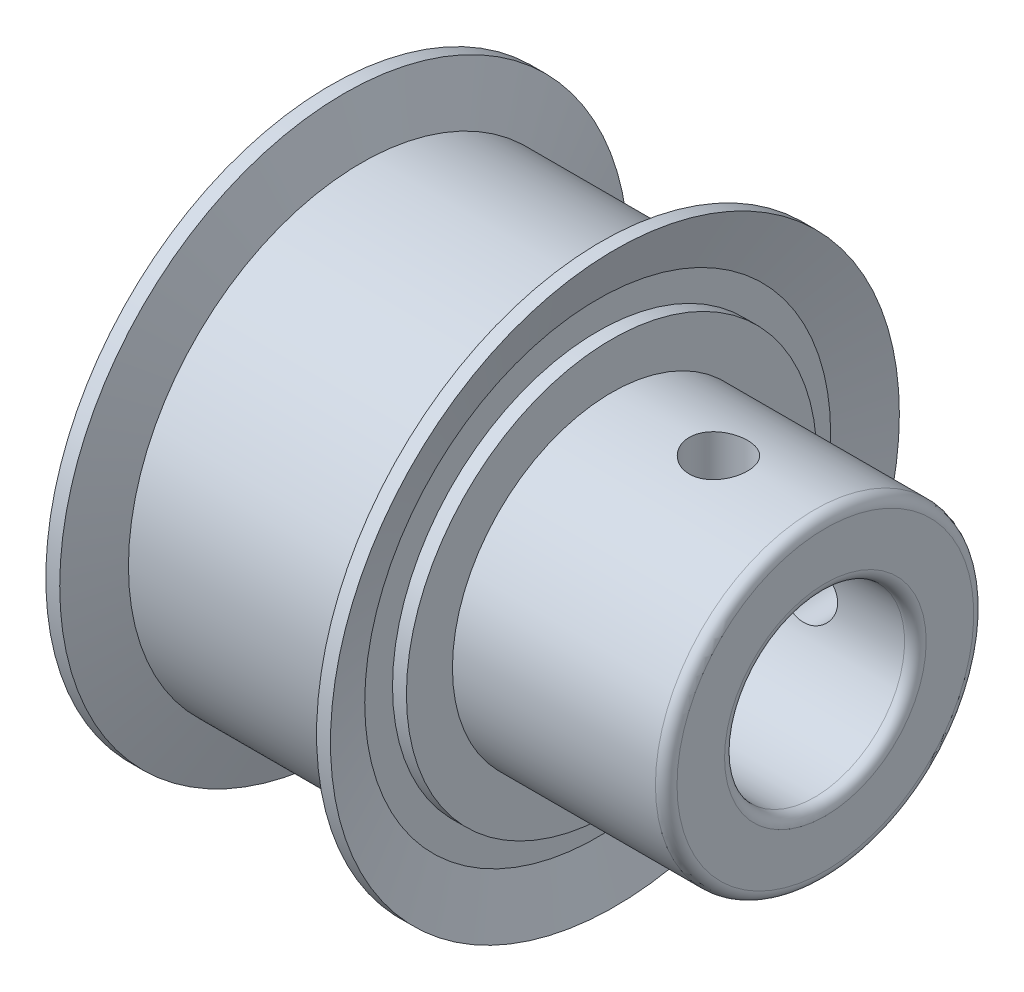
SolidWorks part; units mm, degrees
ref_plane "Front Plane" through (0, 0, 0) normal (0, 0, 1) x (1, 0, 0)
ref_plane "Top Plane" through (0, 0, 0) normal (0, 1, 0) x (1, 0, 0)
ref_plane "Right Plane" through (0, 0, 0) normal (1, 0, 0) x (0, 0, -1)
sketch "Sketch2" plane through (0, 0, 0) normal (0, 0, 1) x (1, 0, 0)
  line L0 (-8.6725, 0) -> (8.6725, 0) construction
  line L1 (-8.6725, 3.175) -> (8.6725, 3.175)
  line L2 (0, 0) -> (0, 8.2169) construction
  line L3 (-8.6725, 3.175) -> (-8.6725, 7.2365)
  line L4 (-7.6921, 8.2169) -> (0.1514, 8.2169)
  line L5 (1.1319, 7.2365) -> (1.1319, 5.6134)
  line L6 (1.1319, 5.6134) -> (8.6725, 5.6134)
  line L7 (8.6725, 0) -> (8.6725, 3.175) construction
  line L8 (-8.6725, 0) -> (-8.6725, 3.175) construction
  line L9 (8.6725, 5.6134) -> (8.6725, 3.175)
  line L11 (-7.6921, 8.2169) -> (-7.6921, 7.2365)
  line L12 (-7.6921, 7.2365) -> (-8.6725, 7.2365)
  line L14 (0.1514, 7.2365) -> (1.1319, 7.2365)
  line L15 (0.1514, 8.2169) -> (0.1514, 7.2365)
  dimension "D1" = 0.9804
  dimension "Bore [A]" = 6.35
  dimension "Hub Diameter [F]" = 11.2268
  dimension "Outside Diameter [B]" = 16.4338
  dimension "Face Width [DD]" = 9.8044
  dimension "Dimension [G]" = 7.5406
revolve "PULLEY" add sketch "Sketch2" angle 360 about L0
sketch "Sketch5" plane through (-7.6921, 0, 0) normal (-1, 0, 0) x (0, 0, 1)
  line L0 (0, 0) -> (0, 11.7317) construction
  line L1 (0, 0) -> (1.3699, 15.6582) construction
  line L2 (0.7494, 8.5652) -> (0.7494, 10.2377) construction
  line L3 (2.0928, 13.9534) -> (1.382, 11.1026) construction
  line L4 (-0.2093, 8.263) -> (0.6841, 8.1884) construction
  line L5 (0.6841, 8.1884) -> (0.6841, 10.709) construction
  line L6 (0, 0) -> (3.2672, 12.1933) construction
  line L7 (0, 0) -> (2.0129, 11.4155) construction
  line L8 (0.717, 8.1856) -> (1.2917, 8.7511)
  line L9 (1.4942, 8.9503) -> (1.7239, 8.9089) construction
  line L10 (1.7239, 8.5701) -> (1.7239, 8.034)
  line L11 (2.1565, 8.0654) -> (3.3617, 7.9647) construction
  line L12 (0.7162, 8.1857) -> (1.7239, 8.1015) construction
  circle A0 centre (0, 0) radius 8.5979 construction
  circle A1 centre (0, 0) radius 8.2169 construction
  arc A2 (1.7239, 8.034) -> (0.7162, 8.1856) centre (0, 0) ccw construction
  circle A3 centre (0, 0) radius 9.0742 construction
  arc A4 (0.8659, 9.0327) -> (0.717, 8.1856) centre (6.8068, 7.5515) ccw construction
  arc A5 (2.2757, 8.7842) -> (2.1259, 7.9371) centre (-3.8135, 9.4242) cw construction
  arc A6 (0.8659, 9.0327) -> (2.2757, 8.7842) centre (0, 0) cw construction
  arc A7 (0.717, 8.1856) -> (1.7239, 8.034) centre (0, 0) cw
  arc A8 (1.7239, 8.5701) -> (1.2917, 8.7511) centre (1.4699, 8.5701) ccw
  circle A9 centre (0, 0) radius 8.2169
  arc A10 (1.7239, 8.034) -> (0.7162, 8.1856) centre (0, 0) ccw
  arc A11 (2.1267, 7.9369) -> (2.1259, 7.9371) centre (0, 0) ccw construction
  arc A12 (2.1267, 7.9369) -> (2.1259, 7.9371) centre (0, 0) ccw
  point P6 (0.7494, 8.5652)
  dimension "D1" = 0.8573
  dimension "Pitch Diameter" = 17.1958
  dimension "D6" = 0.254
  dimension "D2" = 5
  dimension "D3" = 14
  dimension "D4" = 10
  dimension "D7" = 0.402
  dimension "D8" = 0.8064
  dimension "D5" = 0
ref_plane "Plane1" through (-7.6921, 0, 0) normal (-1, 0, 0) x (0, 0, 1)
sketch "Pitch Dia Curve" plane through (-7.6921, 0, 0) normal (-1, 0, 0) x (0, 0, 1)
  circle A0 centre (0, 0) radius 8.5979 construction
  circle A1 centre (0, 0) radius 8.5979 construction
sketch "Sketch4" plane through (0, 0, 0) normal (0, 0, 1) x (1, 0, 0)
  line L0 (-8.1823, 7.2365) -> (-8.1823, 8.2169)
  line L1 (-8.79, 10.033) -> (-8.2998, 10.033)
  line L2 (0, 0) -> (-8.6725, 0) construction
  line L4 (-7.6921, 7.2365) -> (-8.6725, 7.2365) construction
  line L5 (-7.6921, 8.2169) -> (-7.6921, -8.2169) construction
  line L6 (-8.1823, 8.2169) -> (-8.79, 10.033)
  line L7 (-7.6921, 8.2169) -> (-8.2998, 10.033)
  line L8 (-3.7703, 0) -> (-3.7703, 8.2169) construction
  line L9 (0.1514, -8.2169) -> (0.1514, 8.2169) construction
  line L10 (-7.6921, 8.2169) -> (-7.6921, 7.2365)
  line L11 (-7.6921, 7.2365) -> (-8.1823, 7.2365)
  line L12 (0.1514, 8.2169) -> (-7.6921, 8.2169) construction
  line L13 (0.1514, 7.2365) -> (0.6417, 7.2365)
  line L14 (0.1514, 8.2169) -> (0.1514, 7.2365)
  line L15 (-8.6725, 7.2365) -> (-8.6725, -7.2365) construction
  line L18 (0.1514, 8.2169) -> (0.7591, 10.033)
  line L19 (0.6417, 8.2169) -> (1.2494, 10.033)
  line L20 (1.2494, 10.033) -> (0.7591, 10.033)
  line L21 (0.6417, 7.2365) -> (0.6417, 8.2169)
  dimension "Diameter [CC]" = 20.066
  dimension "Length [E]" = 17.4625
revolve "Flange" add sketch "Sketch4" angle 360 about L2
sketch "Sketch3" plane through (0, 0, 0) normal (0, 1, 0) x (1, 0, 0)
  line L0 (1.1319, 0) -> (8.6725, 0) construction
  line L3 (1.1319, -5.6134) -> (1.1319, 5.6134) construction
  line L7 (8.6725, -5.6134) -> (8.6725, 5.6134) construction
  circle A0 centre (4.9022, 0) radius 1.0287
  dimension "Diameter [DI]" = 2.0574
extrude "SCREW HOLE" cut sketch "Sketch3" along normal through all
cosmetic thread "Cosmetic Thread1" parameters "D2"=2.5718
pattern_circular "CirPattern1" count 2 over 90 about axis through (-8.6725, 0, 0) along (1, 0, 0) of "SCREW HOLE"
cosmetic thread "Cosmetic Thread2" parameters "D2"=2.5718
fillet "Fillet1" radius 0.381 3 edges at (-8.6725, 0, 3.175) (8.6725, 0, 3.175) (8.6725, 0, 5.6134)
equation "\"D1@Sketch2\" = \"Face Width [DD]@Sketch2\"*.1"
equation "\"D1@Sketch5\" = (\"Pitch Diameter@Sketch5\"-\"Outside Diameter [B]@Sketch2\")*1.125"
equation "\"D4@Sketch5\" = \"D2@Sketch5\"*2"
equation "\"D2@Cosmetic Thread1\" = \"Diameter [DI]@Sketch3\" * 1.25"
equation "\"D2@Cosmetic Thread2\" = \"Diameter [DI]@Sketch3\"*1.25"
